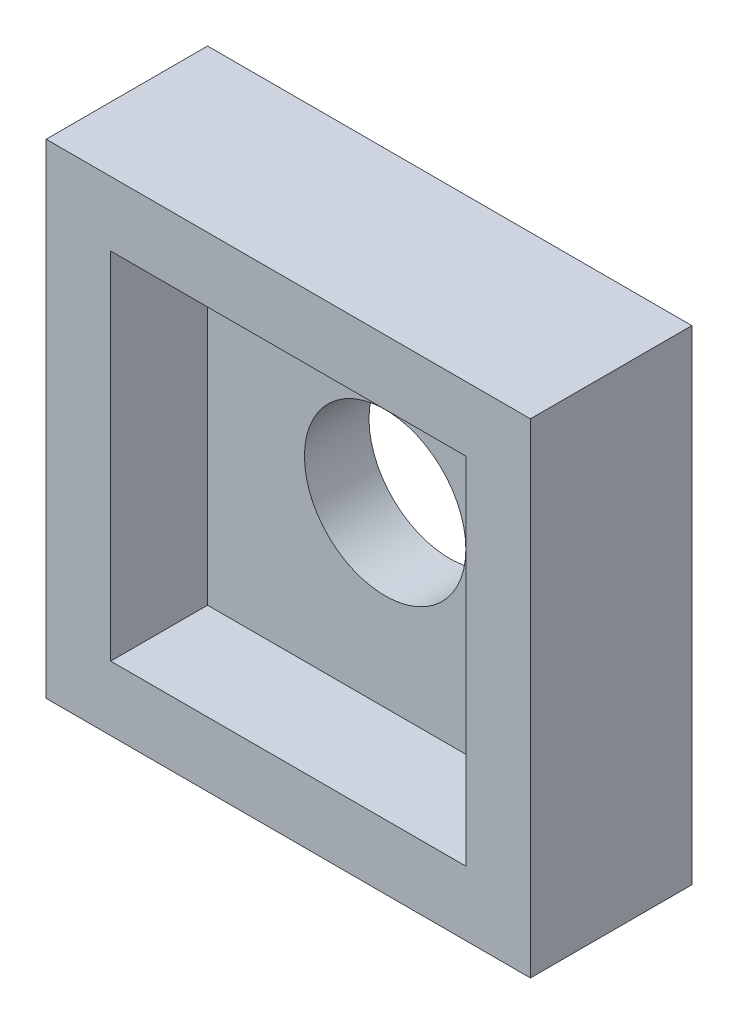
SolidWorks part; units mm, degrees
ref_plane "前视基准面" through (0, 0, 0) normal (0, 0, 1) x (1, 0, 0)
ref_plane "上视基准面" through (0, 0, 0) normal (0, 1, 0) x (1, 0, 0)
ref_plane "右视基准面" through (0, 0, 0) normal (1, 0, 0) x (0, 0, -1)
sketch "草图1" plane through (0, 0, 0) normal (0, 0, 1) x (1, 0, 0)
  line L5 (-7.5, -7.5) -> (7.5, -7.5)
  line L6 (-7.5, -7.5) -> (-7.5, 7.5)
  line L11 (-7.5, 7.5) -> (7.5, 7.5)
  line L12 (7.5, -7.5) -> (7.5, 7.5)
  line L13 (-7.5, -7.5) -> (7.5, 7.5) construction
  line L14 (-7.5, 7.5) -> (7.5, -7.5) construction
  point P0 (0, 0)
  dimension "D1" = 15
  dimension "D2" = 15
extrude "凸台-拉伸2" add sketch "草图1" along normal blind 5
shell "抽壳1" thickness 2
sketch "草图2" plane through (0, 0, 0) normal (0, 0, -1) x (-1, 0, 0)
  circle A0 centre (0, 0) radius 2.5
extrude "切除-拉伸1" cut sketch "草图2" against normal blind 5
